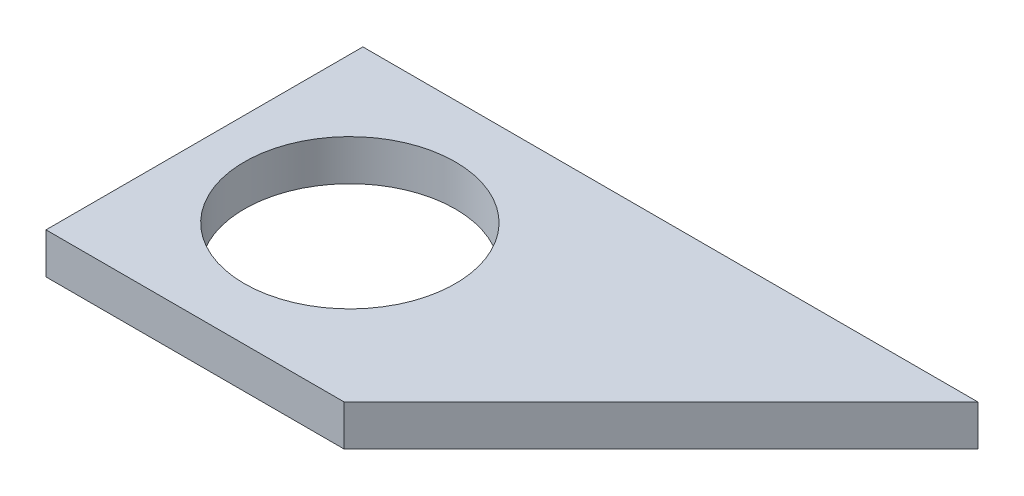
SolidWorks part; units mm, degrees
ref_plane "Front Plane" through (0, 0, 0) normal (0, 0, 1) x (1, 0, 0)
ref_plane "Top Plane" through (0, 0, 0) normal (0, 1, 0) x (1, 0, 0)
ref_plane "Right Plane" through (0, 0, 0) normal (1, 0, 0) x (0, 0, -1)
sketch "Sketch1" plane through (0, 0, 0) normal (0, 1, 0) x (1, 0, 0)
  line L0 (42.4, 0) -> (87.45, 45.05)
  line L1 (0, 0) -> (42.4, 0)
  line L2 (0, 0) -> (0, 45.05)
  line L3 (0, 45.05) -> (52.7975, 45.05)
  line L5 (87.45, 45.05) -> (52.7975, 45.05)
  circle A0 centre (20.73, 22.47) radius 15
  dimension "D4" = 30
  dimension "D5" = 22.47
  dimension "D6" = 20.73
  dimension "D1" = 45.05
  dimension "D2" = 42.4
  dimension "D3" = 135
extrude "Boss-Extrude1" add sketch "Sketch1" along normal blind 5.8
